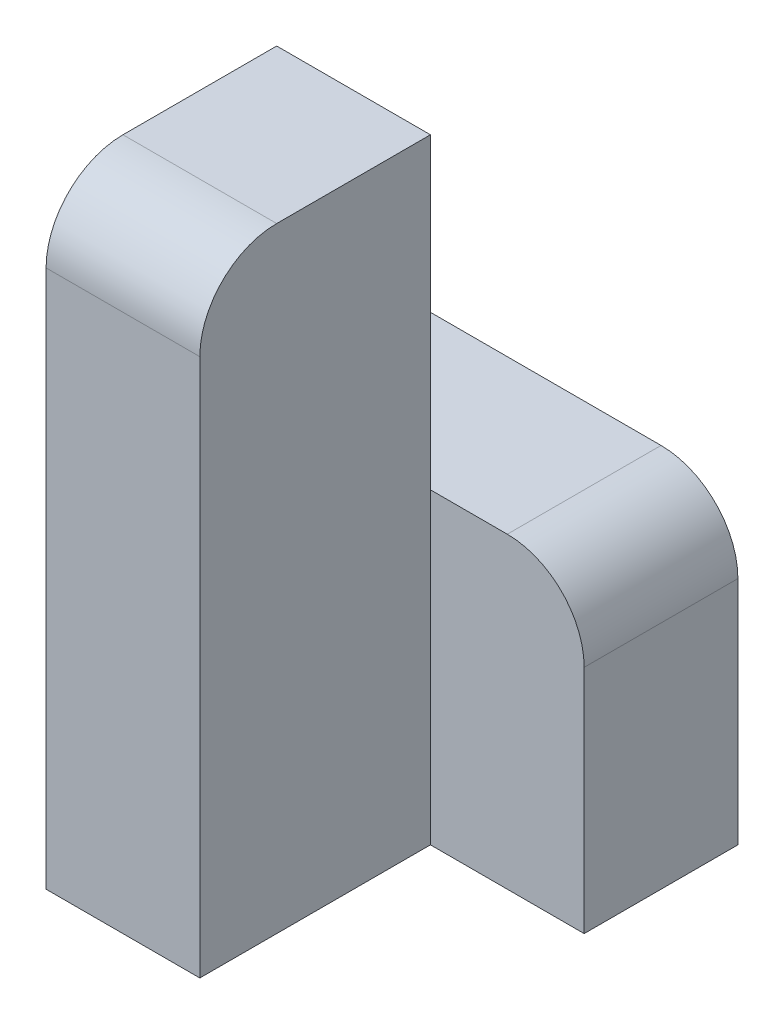
SolidWorks part; units mm, degrees
ref_plane "Front Plane" through (0, 0, 0) normal (0, 0, 1) x (1, 0, 0)
ref_plane "Top Plane" through (0, 0, 0) normal (0, 1, 0) x (1, 0, 0)
ref_plane "Right Plane" through (0, 0, 0) normal (1, 0, 0) x (0, 0, -1)
sketch "Sketch1" plane through (0, 0, 0) normal (0, 0, 1) x (1, 0, 0)
  line L1 (-30, -80) -> (-10, -80)
  line L2 (-10, -80) -> (-10, 0)
  line L3 (-10, 0) -> (-30, 0)
  line L4 (-30, 0) -> (-30, -80)
  dimension "D1" = 20
  dimension "Width" = 80
extrude "Boss-Extrude1" add sketch "Sketch1" along normal blind 30
sketch "Sketch2" plane through (0, 0, 0) normal (0, 0, 1) x (1, 0, 0)
  line L1 (-30, -80) -> (10, -80)
  line L2 (10, -80) -> (10, -40)
  line L3 (10, -40) -> (-30, -40)
  line L4 (-30, -40) -> (-30, -80)
  dimension "D1" = 40
  dimension "Width" = 40
extrude "Boss-Extrude2" add sketch "Sketch2" against normal blind 20
fillet "Fillet1" radius 10 2 edges at (10, -40, -10) (-20, 0, 30)
